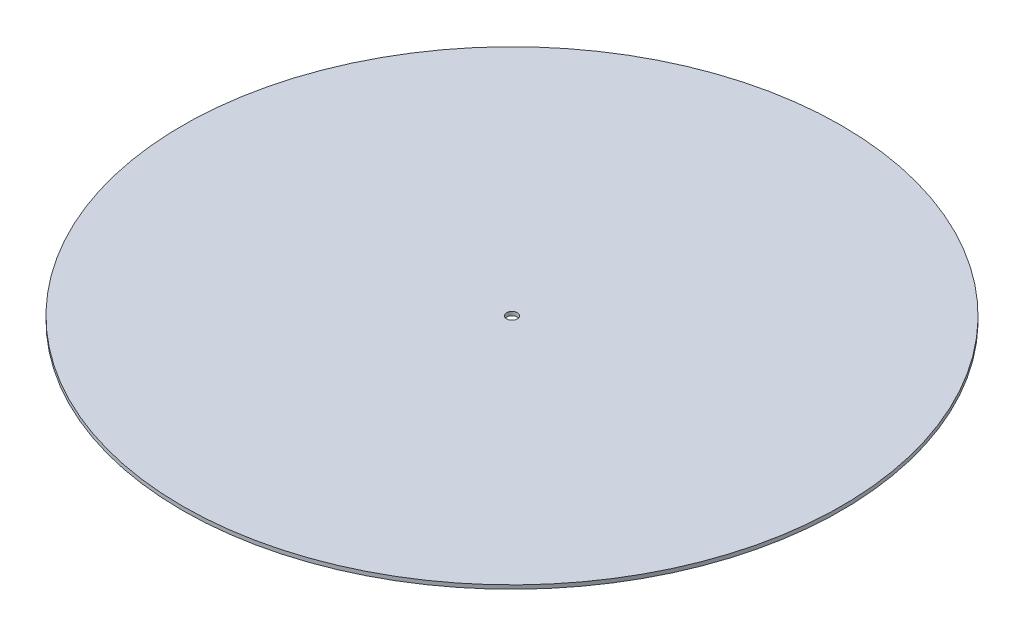
SolidWorks part; units mm, degrees
material "Pine"
ref_plane "Front Plane" through (0, 0, 0) normal (0, 0, 1) x (1, 0, 0)
ref_plane "Top Plane" through (0, 0, 0) normal (0, 1, 0) x (1, 0, 0)
ref_plane "Right Plane" through (0, 0, 0) normal (1, 0, 0) x (0, 0, -1)
sketch "Sketch1" plane through (0, 0, 0) normal (0, 1, 0) x (1, 0, 0)
  circle A0 centre (0, 0) radius 550
  circle A1 centre (0, 0) radius 9
  dimension "D1" = 1100
  dimension "D2" = 18
extrude "Boss-Extrude1" add sketch "Sketch1" along normal blind 6.35
